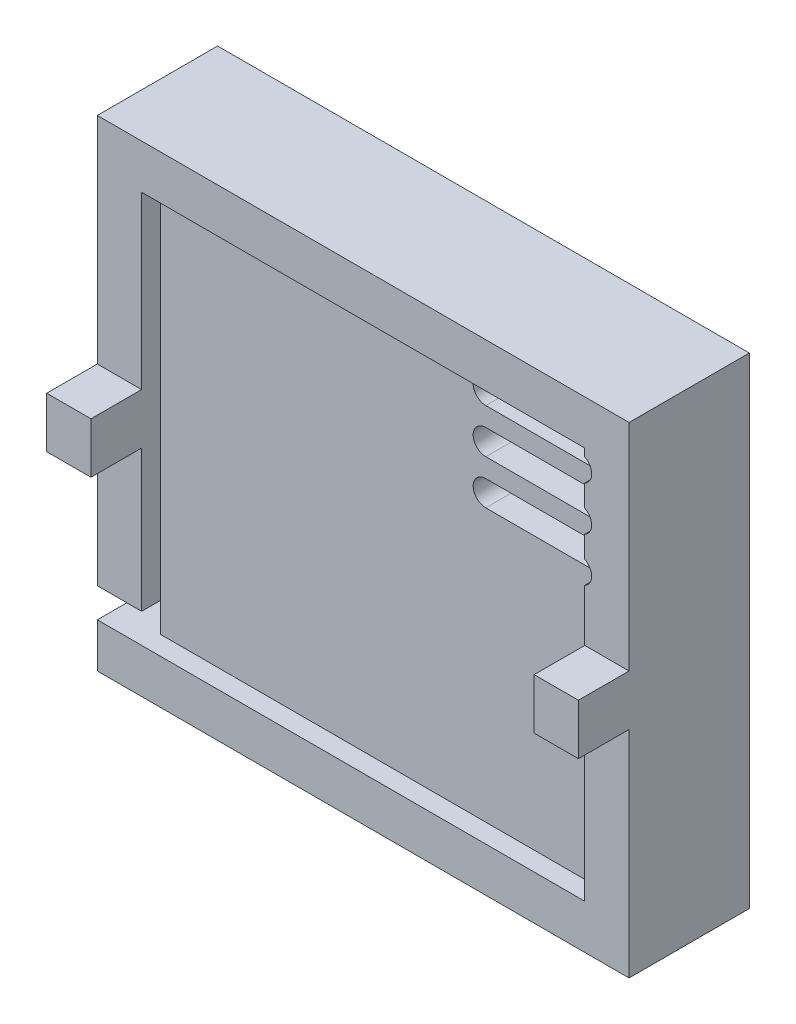
SolidWorks part; units mm, degrees
ref_plane "前视基准面" through (0, 0, 0) normal (0, 0, 1) x (1, 0, 0)
ref_plane "上视基准面" through (0, 0, 0) normal (0, 1, 0) x (1, 0, 0)
ref_plane "右视基准面" through (0, 0, 0) normal (1, 0, 0) x (0, 0, -1)
sketch "草图1" plane through (0, 0, 0) normal (0, 0, 1) x (1, 0, 0)
  line L1 (0, 0) -> (42, 0)
  line L2 (0, 0) -> (0, 38)
  line L3 (0, 38) -> (42, 38)
  line L4 (42, 0) -> (42, 38)
  dimension "D1" = 38
  dimension "D2" = 42
extrude "凸台-拉伸1" add sketch "草图1" along normal blind 3.5
sketch "草图2" plane through (0, 0, 3.5) normal (0, 0, 1) x (1, 0, 0)
  line L0 (0, 19) -> (0, 21)
  line L1 (0, 38) -> (0, 0) construction
  line L2 (42, 19) -> (42, 21)
  line L3 (0, 21) -> (3.5, 21)
  line L4 (0, 21) -> (0, 17)
  line L5 (0, 17) -> (3.5, 17)
  line L6 (3.5, 21) -> (3.5, 17)
  line L7 (42, 0) -> (42, 38) construction
  line L9 (42, 21) -> (38.5, 21)
  line L10 (42, 21) -> (42, 17)
  line L11 (42, 17) -> (38.5, 17)
  line L12 (38.5, 21) -> (38.5, 17)
  line M7 (0, 38) -> (0, 0)
  line M9 (42, 0) -> (42, 38)
  dimension "D1" = 2
  dimension "D2" = 3.5
  dimension "D3" = 4
  dimension "D4" = 2
  dimension "D5" = 4
  dimension "D6" = 3.5
extrude "凸台-拉伸2" add sketch "草图2" along normal blind 4 contours L6 L3 L5 M7 | L9 L12 L11 M9
sketch "草图3" plane through (0, 0, 3.5) normal (0, 0, 1) x (1, 0, 0)
  line L1 (0, 0) -> (3.5, 0) construction
  line L2 (0, 0) -> (0, 3.5) construction
  line L3 (0, 3.5) -> (3.5, 3.5) construction
  line L4 (3.5, 0) -> (3.5, 3.5) construction
  line L5 (3.5, 3.5) -> (38.5, 3.5)
  line L6 (3.5, 3.5) -> (3.5, 34.5)
  line L7 (3.5, 34.5) -> (38.5, 34.5)
  line L8 (38.5, 3.5) -> (38.5, 34.5)
  dimension "D1" = 3.5
  dimension "D2" = 3.5
  dimension "D3" = 31
  dimension "D4" = 35
extrude "切除-拉伸1" cut sketch "草图3" against normal blind 1.5
sketch "草图4" plane through (0, 0, 0) normal (0, 0, -1) x (-1, 0, 0)
  line L0 (-42, 38) -> (0, 38) construction
  line L1 (-42, 0) -> (-38.5, 0) construction
  line L2 (-42, 0) -> (-42, 3.5) construction
  line L3 (-42, 3.5) -> (-38.5, 3.5) construction
  line L4 (-38.5, 0) -> (-38.5, 3.5) construction
  line L5 (-38.5, 3.5) -> (-3.5, 3.5)
  line L6 (-38.5, 3.5) -> (-38.5, 34.5)
  line L7 (-38.5, 34.5) -> (-3.5, 34.5)
  line L8 (-3.5, 3.5) -> (-3.5, 34.5)
  line L9 (-42, 0) -> (0, 0)
  line L10 (-42, 0) -> (-42, 38)
  line L11 (-42, 38) -> (0, 38)
  line L12 (0, 0) -> (0, 38)
  dimension "D1" = 3.5
  dimension "D2" = 3.5
  dimension "D3" = 31
  dimension "D4" = 35
extrude "凸台-拉伸3" add sketch "草图4" along normal blind 4 contours L10 L9 L12 L11 | L6 L5 L8 L7
sketch "草图6" plane through (0, 0, -4) normal (0, 0, -1) x (-1, 0, 0)
  line L1 (-42, 38) -> (0, 38)
  line L2 (-42, 38) -> (-42, 0)
  line L3 (-42, 0) -> (0, 0)
  line L4 (0, 38) -> (0, 0)
extrude "凸台-拉伸4" add sketch "草图6" along normal blind 2
sketch "草图7" plane through (0, 0, 0) normal (-1, 0, 0) x (0, 0, 1)
  line L1 (3.5, 0) -> (0, 0) construction
  line L2 (3.5, 0) -> (3.5, 3.5) construction
  line L3 (3.5, 3.5) -> (0, 3.5) construction
  line L4 (0, 0) -> (0, 3.5) construction
  line L5 (0, 3.5) -> (-4, 3.5)
  line L6 (0, 3.5) -> (0, 28.5)
  line L7 (0, 28.5) -> (-4, 28.5)
  line L8 (-4, 3.5) -> (-4, 28.5)
  dimension "D1" = 3.5
  dimension "D2" = 3.5
  dimension "D3" = 4
  dimension "D4" = 25
extrude "切除-拉伸2" cut sketch "草图7" against normal blind 3.5
sketch "草图8" plane through (0, 0, 0) normal (-1, 0, 0) x (0, 0, 1)
  line L0 (3.5, 17) -> (3.5, 0) construction
  line L1 (0, 3.5) -> (3.5, 3.5)
  line L2 (0, 3.5) -> (0, 5.8318)
  line L3 (0, 5.8318) -> (3.5, 5.8318)
  line L4 (3.5, 3.5) -> (3.5, 5.8318)
extrude "切除-拉伸3" cut sketch "草图8" against normal blind 3.5
sketch "草图9" plane through (0, 0, -6) normal (0, 0, -1) x (-1, 0, 0)
  line L0 (-38.0447, 26) -> (-29.1868, 26) construction
  line L1 (-42, 0) -> (-38.5, 0) construction
  line L2 (-42, 0) -> (-42, 3.5) construction
  line L3 (-42, 3.5) -> (-38.5, 3.5) construction
  line L4 (-38.5, 0) -> (-38.5, 3.5) construction
  line L5 (-38.5, 3.5) -> (-28.5, 3.5) construction
  line L6 (-38.5, 3.5) -> (-38.5, 15.5) construction
  line L7 (-38.5, 15.5) -> (-28.5, 15.5) construction
  line L8 (-28.5, 3.5) -> (-28.5, 15.5) construction
  line L9 (-38.0447, 27) -> (-29.1868, 27)
  line L10 (-38.0447, 25) -> (-29.1868, 25)
  line L11 (-38.0447, 29.5) -> (-29.1868, 29.5) construction
  line L12 (-38.0447, 30.5) -> (-29.1868, 30.5)
  line L13 (-38.0447, 28.5) -> (-29.1868, 28.5)
  line L14 (-38.0447, 33) -> (-29.1868, 33) construction
  line L15 (-38.0447, 34) -> (-29.1868, 34)
  line L16 (-38.0447, 32) -> (-29.1868, 32)
  arc A0 (-38.0447, 27) -> (-38.0447, 25) centre (-38.0447, 26) ccw
  arc A1 (-29.1868, 25) -> (-29.1868, 27) centre (-29.1868, 26) ccw
  arc A2 (-38.0447, 30.5) -> (-38.0447, 28.5) centre (-38.0447, 29.5) ccw
  arc A3 (-29.1868, 28.5) -> (-29.1868, 30.5) centre (-29.1868, 29.5) ccw
  arc A4 (-38.0447, 34) -> (-38.0447, 32) centre (-38.0447, 33) ccw
  arc A5 (-29.1868, 32) -> (-29.1868, 34) centre (-29.1868, 33) ccw
  point P10 (-33.6157, 26)
  point P15 (-33.6157, 29.5)
  point P22 (-33.6157, 33)
  dimension "D5" = 1
  dimension "D6" = 1
  dimension "D7" = 1
  dimension "D1" = 3.5
  dimension "D2" = 3.5
  dimension "D3" = 10
  dimension "D4" = 12
extrude "切除-拉伸4" cut sketch "草图9" against normal blind 10 contours L16 A5 L15 A4 | L13 A3 L12 A2 | L10 A1 L9 A0
sketch "草图10" plane through (0, 0, 0) normal (0, 0, -1) x (-1, 0, 0)
  line L3 (-27.9839, 34.5) -> (-26.1454, 34.5)
  line L6 (-27.9839, 34.5) -> (-26.4839, 34.5)
  line L7 (-27.9839, 34.5) -> (-27.9839, 3.5)
  line L8 (-27.9839, 3.5) -> (-26.4839, 3.5)
  line L9 (-26.4839, 34.5) -> (-26.4839, 3.5)
  line L10 (-27.9839, 3.5) -> (-26.1454, 3.5)
  line M22 (-38.5, 3.5) -> (-3.5, 3.5)
  dimension "D2" = 1.5
extrude "凸台-拉伸5" add sketch "草图10" along normal blind 5 contours L9 L3 L7 M22
